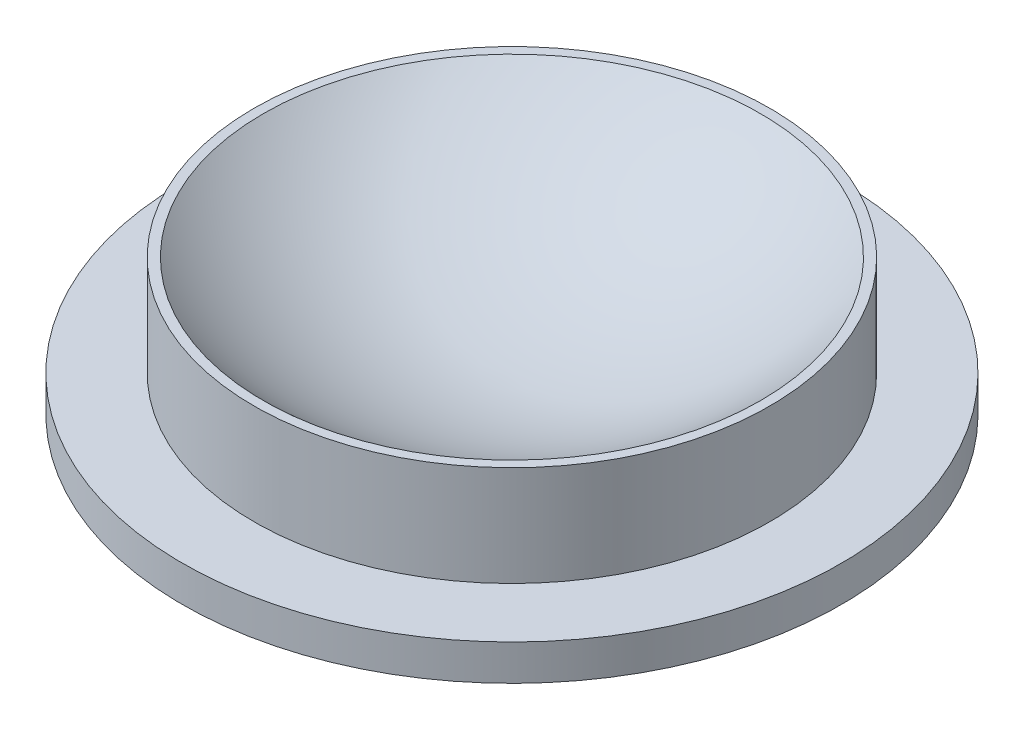
SolidWorks part; units mm, degrees
ref_plane "Спереди" through (0, 0, 0) normal (0, 0, 1) x (1, 0, 0)
ref_plane "Сверху" through (0, 0, 0) normal (0, 1, 0) x (1, 0, 0)
ref_plane "Справа" through (0, 0, 0) normal (1, 0, 0) x (0, 0, -1)
sketch "Эскиз1" plane through (0, 0, 0) normal (0, 0, 1) x (1, 0, 0)
  line L0 (0, -50) -> (0, -55)
  line L1 (0, -55) -> (46, -55)
  line L2 (46, -55) -> (46, -50)
  line L3 (36, -36) -> (34.6987, -36)
  line L4 (36, -36) -> (36, -50)
  line L5 (36, -50) -> (46, -50)
  line L6 (0, 0) -> (35.3553, -35.3553) construction
  arc A0 (0, -50) -> (35.3553, -35.3553) centre (0, 0) ccw construction
  arc A1 (0, -50) -> (34.6987, -36) centre (0, 0) ccw
  point P1 (34.6987, -36)
  dimension "D1" = 100
  dimension "D2" = 19
  dimension "D3" = 5
  dimension "D4" = 45
  dimension "D5" = 10
  dimension "D6" = 5
  dimension "D7" = 1.3013
revolve "Повернуть2" add sketch "Эскиз1" angle 360 about L0
